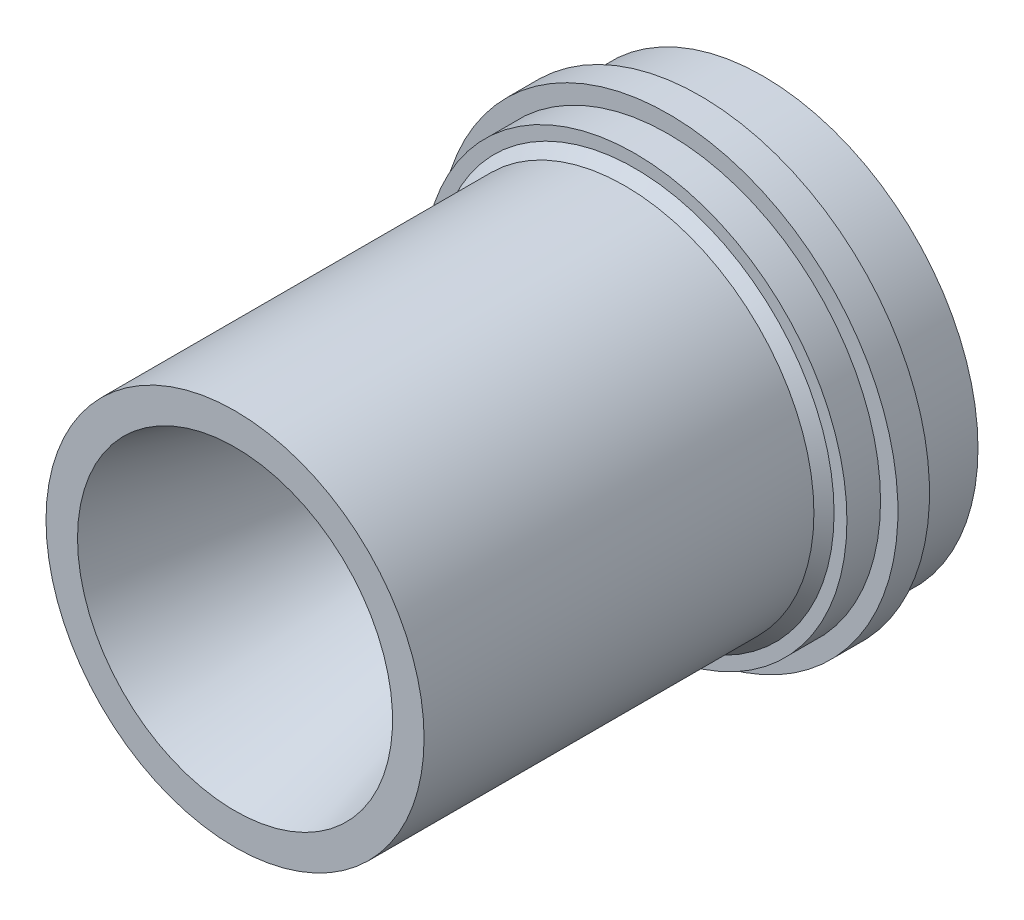
SolidWorks part; units mm, degrees
material "C (Graphite)"
ref_plane "Front Plane" through (0, 0, 0) normal (0, 0, 1) x (1, 0, 0)
ref_plane "Top Plane" through (0, 0, 0) normal (0, 1, 0) x (1, 0, 0)
ref_plane "Right Plane" through (0, 0, 0) normal (1, 0, 0) x (0, 0, -1)
sketch "Sketch1" plane through (0, 0, 0) normal (1, 0, 0) x (0, 0, -1)
  line L0 (-79.8322, 28.575) -> (-20.9042, 28.575)
  line L1 (-20.9042, 28.575) -> (-19.3802, 30.099)
  line L2 (-19.3802, 30.099) -> (-19.3802, 32.0421)
  line L3 (-19.3802, 32.0421) -> (-14.3002, 32.0421)
  line L4 (-14.3002, 32.0421) -> (-14.3002, 34.671)
  line L5 (-14.3002, 34.671) -> (-9.525, 34.671)
  line L6 (-9.525, 34.671) -> (-9.525, 32.4739)
  line L7 (-9.525, 32.4739) -> (0, 32.4739)
  line L8 (0, 32.4739) -> (0, 26.5811)
  line L9 (0, 26.5811) -> (-6.1959, 15.8494)
  line L10 (-18.6545, 8.6995) -> (-23.4297, 8.6995)
  line L11 (-23.4297, 8.6995) -> (-79.8322, 23.8125)
  line L12 (-79.8322, 23.8125) -> (-79.8322, 28.575)
  line L13 (0, 0) -> (-36.7731, 0) construction
  line L14 (0, 0) -> (0, 26.5811) construction
  arc A0 (-6.1959, 15.8494) -> (-18.6545, 8.6995) centre (-18.5803, 22.9995) cw
  point P18 (0, 0)
  dimension "D11" = 14.3002
  dimension "D1" = 15
  dimension "D2" = 28.575
  dimension "D3" = 23.8125
  dimension "D4" = 8.6995
  dimension "D5" = 60
  dimension "D6" = 79.8322
  dimension "D7" = 20.9042
  dimension "D8" = 19.3802
  dimension "D9" = 14.3002
  dimension "D10" = 9.525
  dimension "D12" = 26.5811
  dimension "D13" = 4.7752
  dimension "D14" = 34.671
  dimension "D15" = 32.4739
  dimension "D16" = 30.099
  dimension "D17" = 32.0421
revolve "Revolve1" add sketch "Sketch1" angle 360 about L13
